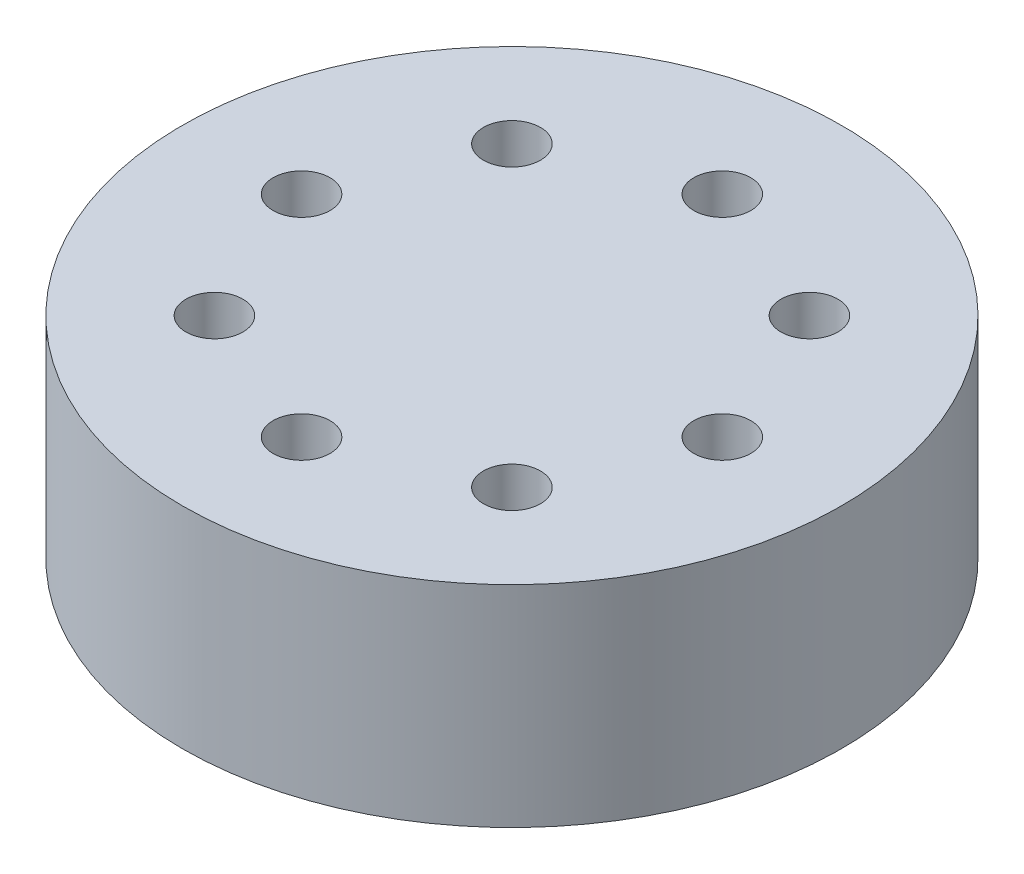
SolidWorks part; units mm, degrees
material "Ceramic Porcelain"
ref_plane "Front Plane" through (0, 0, 0) normal (0, 0, 1) x (1, 0, 0)
ref_plane "Top Plane" through (0, 0, 0) normal (0, 1, 0) x (1, 0, 0)
ref_plane "Right Plane" through (0, 0, 0) normal (1, 0, 0) x (0, 0, -1)
sketch "Sketch1" plane through (0, 0, 0) normal (0, 1, 0) x (1, 0, 0)
  circle A0 centre (0, 0) radius 2.35
  circle A1 centre (0, 1.5) radius 0.2032
  circle A2 centre (1.0607, 1.0607) radius 0.2032
  circle A3 centre (1.5, 0) radius 0.2032
  circle A4 centre (1.0607, -1.0607) radius 0.2032
  circle A5 centre (0, -1.5) radius 0.2032
  circle A6 centre (-1.0607, -1.0607) radius 0.2032
  circle A7 centre (-1.5, 0) radius 0.2032
  circle A8 centre (-1.0607, 1.0607) radius 0.2032
  point P21 (0, 0)
  point P22 (0, 0)
  dimension "D1" = 1.5
  dimension "D3" = 0.4064
  dimension "D4" = 4.7
  dimension "D2" = 8
extrude "Boss-Extrude1" add sketch "Sketch1" along normal blind 1.5
sketch "Sketch2" plane through (0, 1.5, 0) normal (0, 1, 0) x (1, 0, 0)
  circle A0 centre (0, 0) radius 0.75 construction
  dimension "D1" = 0.75
